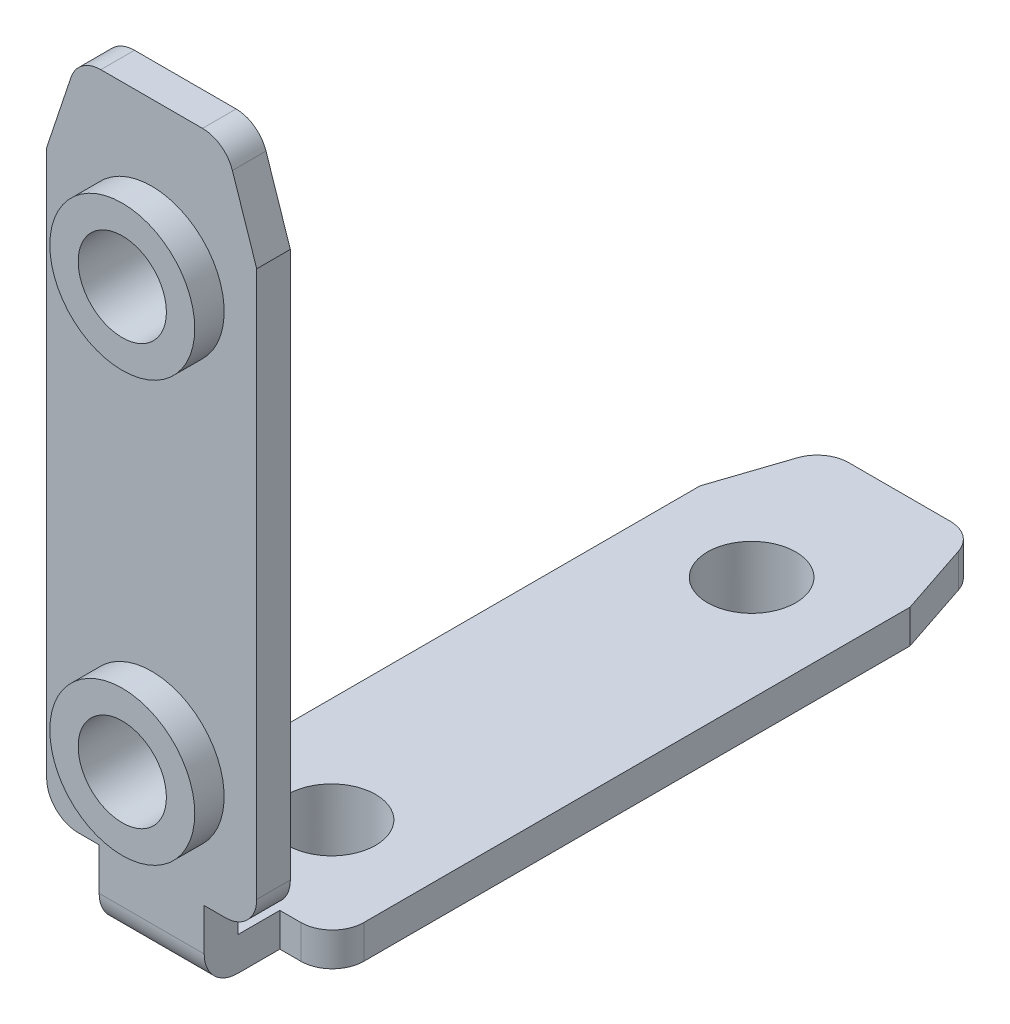
SolidWorks part; units mm, degrees
material "Plain Carbon Steel"
ref_plane "Front Plane" through (0, 0, 0) normal (0, 0, 1) x (1, 0, 0)
ref_plane "Top Plane" through (0, 0, 0) normal (0, 1, 0) x (1, 0, 0)
ref_plane "Right Plane" through (0, 0, 0) normal (1, 0, 0) x (0, 0, -1)
sketch "Sketch1" plane through (0, 0, 0) normal (0, 0, 1) x (1, 0, 0)
  line L0 (-10, 0) -> (0, 0) construction
  line L1 (0, 0) -> (0, 34) construction
  line L2 (-3.5, 2) -> (-2.5, 2)
  line L3 (-2.5, 2) -> (-2.5, 0)
  line L4 (-5, 3.5) -> (-5, 29.5)
  line L5 (-5, 29.5) -> (-3.8419, 32.9743)
  line L6 (-2.4189, 34) -> (2.4189, 34)
  line L7 (5, 29.5) -> (3.8419, 32.9743)
  line L8 (5, 3.5) -> (5, 29.5)
  line L9 (2.5, 2) -> (2.5, 0)
  line L10 (3.5, 2) -> (2.5, 2)
  line L11 (-2.5, 0) -> (2.5, 0)
  arc A0 (5, 3.5) -> (3.5, 2) centre (3.5, 3.5) cw
  arc A1 (-3.5, 2) -> (-5, 3.5) centre (-3.5, 3.5) cw
  arc A3 (-3.8419, 32.9743) -> (-2.4189, 34) centre (-2.4189, 32.5) cw
  arc A4 (3.8419, 32.9743) -> (2.4189, 34) centre (2.4189, 32.5) ccw
  point P16 (5, 2)
  point P19 (-5, 2)
  point P30 (-3.5, 34)
  point P33 (3.5, 34)
  dimension "D4" = 7
  dimension "D8" = 1.5
  dimension "D7" = 1.5
  dimension "D1" = 2
  dimension "D2" = 34
  dimension "D3" = 10
  dimension "D5" = 4.5
  dimension "D6" = 5
extrude "Boss-Extrude1" add sketch "Sketch1" along normal blind 1.6
sketch "Sketch2" plane through (0, 0, 1.6) normal (0, 0, 1) x (1, 0, 0)
  line L0 (-10, 0) -> (0, 0) construction
  line L2 (0, 0) -> (0, 34) construction
  line L3 (2.4189, 34) -> (-2.4189, 34) construction
  circle A0 centre (0, 6.96) radius 3.45
  circle A1 centre (0, 26.96) radius 3.45
  dimension "D1" = 6.9
  dimension "D3" = 6.96
  dimension "D2" = 20
extrude "Boss-Extrude2" add sketch "Sketch2" along normal blind 1.4
hole_wizard "M5x0.8 Tapped Hole1" positions "Sketch4" profile "Sketch3" tap size "M5x0.8" standard "ANSI Metric" end condition through all
sketch "Sketch4" plane through (0, 0, 3) normal (0, 0, 1) x (1, 0, 0)
  point P0 (0, 26.96)
  point P3 (0, 6.96)
sketch "Sketch3" plane through (0, 26.96, 3) normal (1, 0, 0) x (0, -1, 0)
  line L0 (0, 0) -> (0, 37)
  line L1 (0, 37) -> (2.1, 37)
  line L2 (2.1, 37) -> (2.1, 0)
  line L5 (2.1, 0) -> (0, 0)
  line L11 (0, -6.35) -> (0, 107.95) construction
  dimension "Thru Tap Drill Dia." = 4.2
  dimension "Thru Tap Drill Depth" = 37
cosmetic thread "Hole Thread3" parameters "D2"=5
cosmetic thread "Hole Thread4" parameters "D2"=5
ref_plane "Plane1" through (0, 0, 0) normal (0, -0.7071, -0.7071) x (1, 0, 0)
sketch "Sketch5" plane through (2.5, 0, 0) normal (1, 0, 0) x (0, 0, -1)
  line L0 (0, 0) -> (-1.6, 0)
  line L1 (0, -1.6) -> (0, 0)
  arc A0 (-1.6, 0) -> (0, -1.6) centre (0, 0) ccw
extrude "Boss-Extrude3" add sketch "Sketch5" against normal up to surface (5 mm away) up to face at (-2.5, 1, 0.8)
mirror "Mirror4" about plane through (0, 0, 0) normal (0, -0.7071, -0.7071) of "M5x0.8 Tapped Hole1", "Boss-Extrude2", "Boss-Extrude1"
